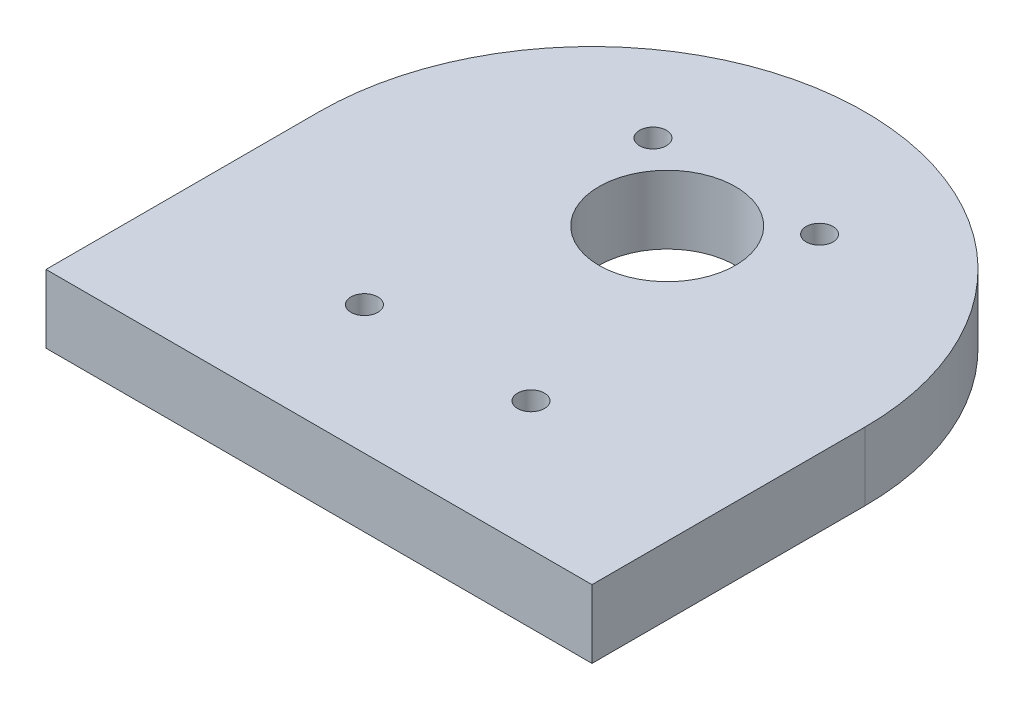
SolidWorks part; units mm, degrees
ref_plane "Front Plane" through (0, 0, 0) normal (0, 0, 1) x (1, 0, 0)
ref_plane "Top Plane" through (0, 0, 0) normal (0, 1, 0) x (1, 0, 0)
ref_plane "Right Plane" through (0, 0, 0) normal (1, 0, 0) x (0, 0, -1)
sketch "Sketch3" plane through (0, 0, 0) normal (0, 1, 0) x (1, 0, 0)
  line L0 (-25.4, 0) -> (-25.4, -25.4)
  line L1 (-25.4, -25.4) -> (0, -25.4)
  line L2 (0, -25.4) -> (25.4, -25.4)
  line L3 (25.4, -25.4) -> (25.4, 0)
  arc A0 (25.4, 0) -> (-25.4, 0) centre (0, 0) ccw
  circle A1 centre (0, 7) radius 6.35
  circle A2 centre (7.75, 13.4234) radius 1.25
  circle A3 centre (-7.75, 13.4234) radius 1.25
  circle A4 centre (-7.75, -13.4234) radius 1.25
  circle A6 centre (7.75, 13.4234) radius 1.25 construction
  circle A11 centre (0, 7) radius 6.175 construction
  circle A12 centre (-7.75, 13.4234) radius 1.25 construction
  circle A13 centre (-7.75, -13.4234) radius 1.25 construction
  circle A14 centre (7.75, -13.4234) radius 1.25
  circle A15 centre (7.75, -13.4234) radius 1.25 construction
  dimension "D1" = 12.7
  dimension "D2" = 25.4
extrude "Boss-Extrude4" add sketch "Sketch3" along normal mid plane 6.35
